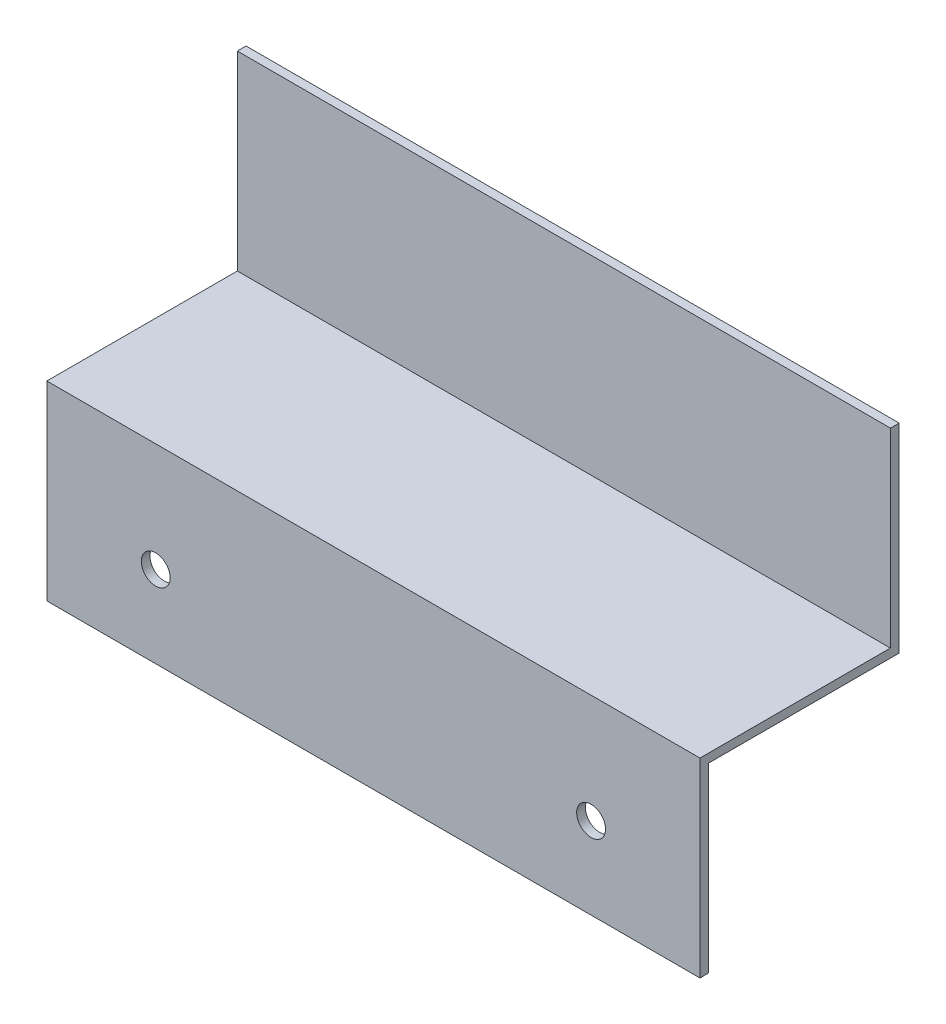
SolidWorks part; units mm, degrees
material "5052-H32"
ref_plane "Front Plane" through (0, 0, 0) normal (0, 0, 1) x (1, 0, 0)
ref_plane "Top Plane" through (0, 0, 0) normal (0, 1, 0) x (1, 0, 0)
ref_plane "Right Plane" through (0, 0, 0) normal (1, 0, 0) x (0, 0, -1)
sketch "Sketch1" plane through (0, 0, 0) normal (1, 0, 0) x (0, 0, -1)
  line L0 (0, 0) -> (0, -44.45)
  line L1 (0, -44.45) -> (-44.45, -44.45)
  line L2 (-44.45, -44.45) -> (-44.45, -88.9)
  line L3 (2.032, 0) -> (2.032, -46.482)
  line L4 (2.032, -46.482) -> (-42.418, -46.482)
  line L5 (-42.418, -46.482) -> (-42.418, -88.9)
  line L6 (-44.45, -88.9) -> (-42.418, -88.9)
  line L7 (0, 0) -> (2.032, 0)
  dimension "D1" = 2.032
  dimension "D2" = 44.45
  dimension "D3" = 88.9
  dimension "D4" = 44.45
extrude "Boss-Extrude1" add sketch "Sketch1" along normal blind 152.4
fillet "Fillet1" [suppressed] radius 2.032
fillet "Fillet2" [suppressed] radius 4.064
fillet "Fillet3" [suppressed] radius 3.175
sketch "Sketch2" plane through (0, 0, 44.45) normal (0, 0, 1) x (1, 0, 0)
  line L0 (152.4, -88.9) -> (0, -88.9) construction
  line L1 (0, -44.45) -> (0, -88.9) construction
  circle A0 centre (25.4, -69.85) radius 3.3655
  circle A1 centre (127, -69.85) radius 3.3655
  dimension "D1" = 19.05
  dimension "D4" = 6.731
  dimension "D2" = 25.4
  dimension "D3" = 127
extrude "Cut-Extrude1" cut sketch "Sketch2" against normal through all
